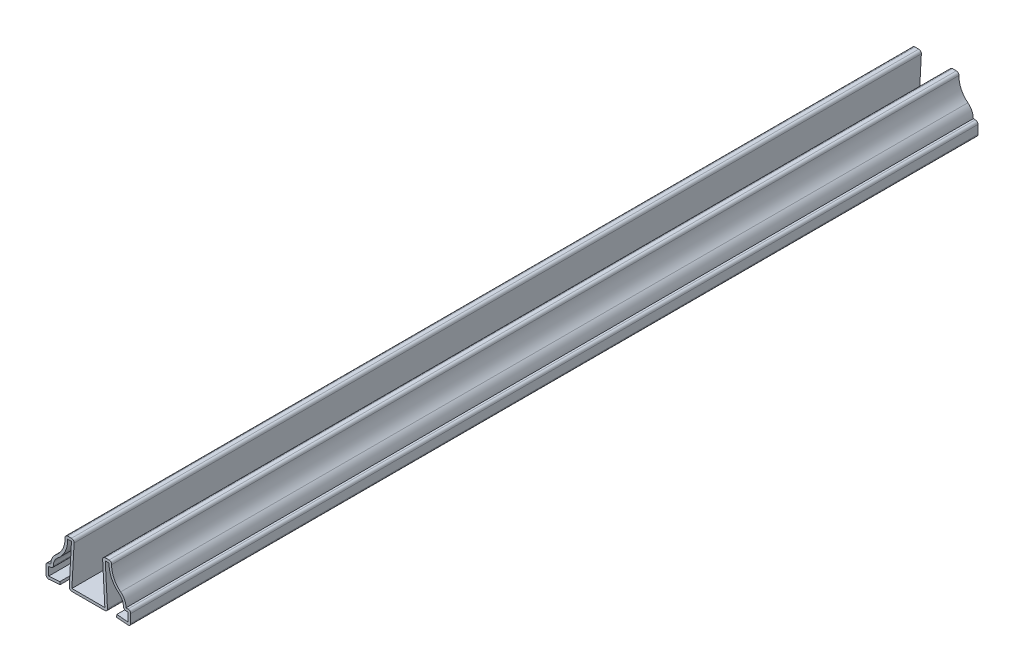
SolidWorks part; units mm, degrees
ref_plane "Front Plane" through (0, 0, 0) normal (0, 0, 1) x (1, 0, 0)
ref_plane "Top Plane" through (0, 0, 0) normal (0, 1, 0) x (1, 0, 0)
ref_plane "Right Plane" through (0, 0, 0) normal (1, 0, 0) x (0, 0, -1)
sketch "Sketch1" plane through (0, 0, 0) normal (0, 0, 1) x (1, 0, 0)
  line L0 (0, 0) -> (0, 13.0947) construction
  line L1 (-14.2875, 0) -> (-9.525, 0.3969)
  line L2 (-14.2875, 0) -> (-14.2875, 4.7625)
  line L3 (-14.2875, 4.7625) -> (-12.7, 4.7625)
  line L4 (-7.9375, 15.875) -> (-4.7625, 15.875)
  line L5 (-4.7625, 15.875) -> (-5.5562, 1.2859)
  line L6 (-5.5562, 1.2859) -> (5.5562, 1.2859)
  line L7 (4.7625, 15.875) -> (5.5562, 1.2859)
  line L8 (7.9375, 15.875) -> (4.7625, 15.875)
  line L9 (14.2875, 4.7625) -> (12.7, 4.7625)
  line L10 (14.2875, 0) -> (14.2875, 4.7625)
  line L11 (14.2875, 0) -> (9.525, 0.3969)
  arc A0 (-12.7, 4.7625) -> (-10.8835, 8.5045) centre (-7.9375, 4.7625) cw
  arc A1 (-10.8835, 8.5045) -> (-7.9375, 15.875) centre (-15.7936, 14.7411) ccw
  arc A2 (10.8835, 8.5045) -> (7.9375, 15.875) centre (15.7936, 14.7411) cw
  arc A3 (12.7, 4.7625) -> (10.8835, 8.5045) centre (7.9375, 4.7625) ccw
  point P11 (0, 0)
  point P15 (0, 0)
  point P16 (0, 0)
  point P17 (-6.7558, 5.3861)
  point P18 (-5.5562, 2.7254)
  point P19 (-7.1854, 3.4446)
  point P20 (-8.6126, 0.3969)
  point P21 (0, 0)
  point P22 (-9.7414, 0.3969)
  point P23 (-10.8951, 8.7589)
  point P24 (-7.9375, 6.7488)
  point P31 (0, 1.2859)
extrude "Extrude-Thin1" add sketch "Sketch1" against normal blind 285.75 thin thin type one direction wall 0.889
fillet "Fillet1" radius 0.889 12 edges at (14.2875, 0, -142.875) (14.2875, 4.7625, -142.875) (4.7625, 15.875, -142.875) (7.9375, 15.875, -142.875) (6.4949, 0.3969, -142.875) (-6.4949, 0.3969, -142.875) (-14.2875, 0, -142.875) (-14.2875, 4.7625, -142.875) (-11.7076, 3.8735, -142.875) (-7.9375, 15.875, -142.875) (-4.7625, 15.875, -142.875) (11.7076, 3.8735, -142.875)
equation "\"D1@Extrude-Thin1\"=\"D7@Sketch1\"*10"
